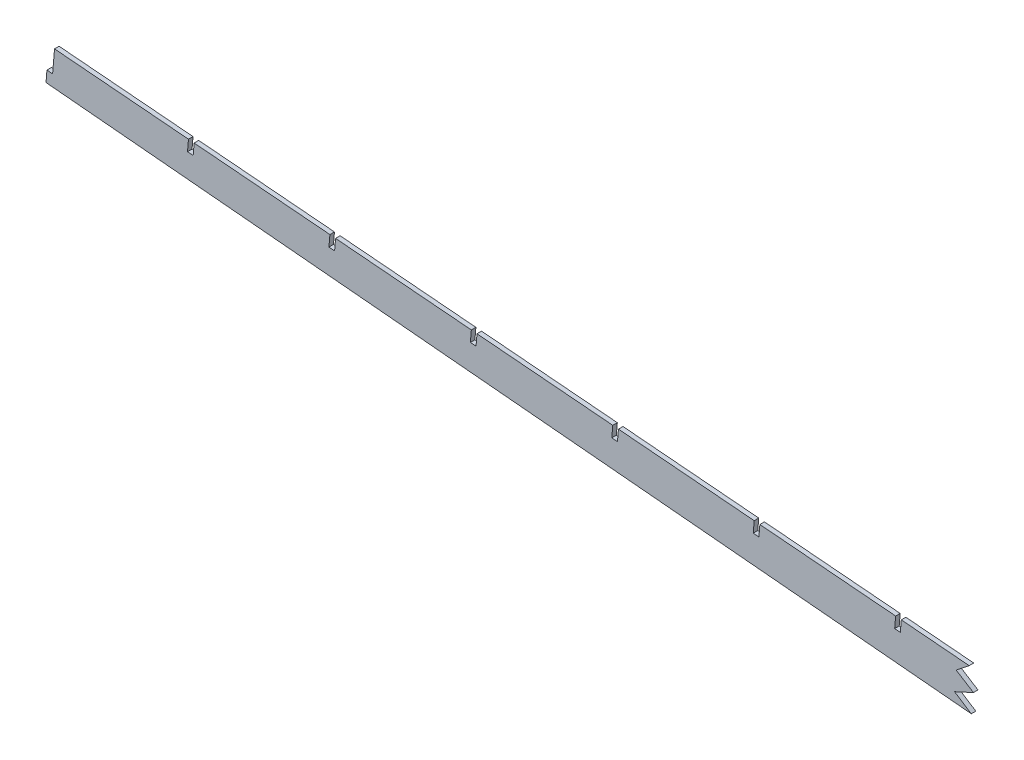
SolidWorks part; units mm, degrees
ref_plane "Front Plane" through (0, 0, 0) normal (0, 0, 1) x (1, 0, 0)
ref_plane "Top Plane" through (0, 0, 0) normal (0, 1, 0) x (1, 0, 0)
ref_plane "Right Plane" through (0, 0, 0) normal (1, 0, 0) x (0, 0, -1)
sketch "Sketch1" plane through (0, 0, 0) normal (0, 0, 1) x (1, 0, 0)
  line L0 (-949.6524, 80.0757) -> (-9.8872, -5.2596)
  line L1 (-945.9572, 86.1378) -> (-949.6524, 80.0757)
  line L8 (-6.7234, -5.5253) -> (-5.1293, 13.4579)
  line L9 (-5.1293, 13.4579) -> (-8.2932, 13.7235)
  line L10 (-8.2932, 13.7235) -> (-9.8872, -5.2596)
  line L11 (-9.8872, -5.2596) -> (-6.7234, -5.5253)
  line L12 (3.175, -5.8337) -> (3.175, 13.2163)
  line L13 (3.175, 13.2163) -> (0, 13.2163)
  line L14 (0, 13.2163) -> (0, -5.8337)
  line L15 (0, -5.8337) -> (3.175, -5.8337)
  line L17 (-943.1142, 119.9943) -> (-945.9572, 86.1378)
  line L18 (-945.9572, 86.1378) -> (-9.8872, -5.2596)
  line L19 (-6.7234, -5.5253) -> (0, -5.8337)
  line L20 (3.175, -5.8337) -> (152.4, -5.8337)
  line L21 (152.4, -5.8337) -> (152.4, 11.9463)
  line L22 (152.4, 11.9463) -> (69.85, 11.9463)
  line L23 (69.85, 11.9463) -> (25.4, 19.5663)
  line L24 (25.4, 19.5663) -> (-1.9861, 19.5663)
  line L25 (-1.9861, 19.5663) -> (-944.8986, 98.7448)
  line L26 (0, 13.2163) -> (0, 19.5663)
  line L27 (3.175, 13.2163) -> (3.175, 19.5663)
  line L28 (-5.1293, 13.4579) -> (-4.598, 19.7856)
  line L29 (-8.2932, 13.7235) -> (-7.7618, 20.0513)
  line L30 (-8.2932, 13.7235) -> (-945.4292, 92.426)
  line L31 (15.875, 19.5663) -> (15.875, 14.4863)
  line L32 (15.875, 14.4863) -> (19.05, 14.4863)
  line L33 (19.05, 14.4863) -> (19.05, 19.5663)
  line L34 (76.2, 6.8663) -> (76.2, 11.9463)
  line L35 (76.2, 6.8663) -> (79.375, 6.8663)
  line L36 (79.375, 6.8663) -> (79.375, 11.9463)
  line L37 (92.075, 11.9463) -> (92.075, 6.8663)
  line L38 (92.075, 6.8663) -> (95.25, 6.8663)
  line L39 (95.25, 6.8663) -> (95.25, 11.9463)
  line L40 (136.525, 11.9463) -> (136.525, 6.8663)
  line L41 (136.525, 6.8663) -> (139.7, 6.8663)
  line L42 (139.7, 6.8663) -> (139.7, 11.9463)
  line L44 (-949.6524, 80.0757) -> (-949.1211, 86.4035)
  line L45 (-949.1211, 86.4035) -> (-945.959, 86.1163)
  dimension "D1" = 25.4
  dimension "D2" = 6.35
extrude "Boss-Extrude1" add sketch "Sketch1" along normal blind 2.54
sketch "Sketch2" plane through (0, 0, 2.54) normal (0, 0, 1) x (1, 0, 0)
  line L1 (-76.483, 72.8473) -> (-82.5095, 1.0799)
  line L3 (-155.6446, 77.1971) -> (-161.4339, 8.255)
  line L5 (-234.8005, 81.6162) -> (-240.3617, 15.3891)
  line L7 (-313.9625, 85.9617) -> (-319.2865, 22.5591)
  line L9 (-393.1191, 90.3714) -> (-398.2146, 29.6908)
  line L11 (-472.2837, 94.686) -> (-477.1388, 36.8682)
  line L13 (-551.4418, 99.0783) -> (-556.0668, 44.0001)
  line L15 (-630.6082, 103.3716) -> (-634.991, 51.1773)
  line L17 (-709.7674, 107.7507) -> (-713.9195, 58.3043)
  line L19 (-788.9364, 112.0121) -> (-792.8436, 65.483)
  line L21 (-868.0976, 116.3681) -> (-871.7723, 72.6069)
  line L23 (-73.3191, 72.5816) -> (-79.3456, 0.8143)
  line L25 (-152.4808, 76.9314) -> (-158.27, 7.9893)
  line L27 (-231.6366, 81.3506) -> (-237.1978, 15.1234)
  line L29 (-310.7986, 85.696) -> (-316.1227, 22.2934)
  line L31 (-389.9552, 90.1057) -> (-395.0507, 29.4251)
  line L33 (-469.1198, 94.4203) -> (-473.9749, 36.6025)
  line L35 (-548.2779, 98.8126) -> (-552.903, 43.7344)
  line L37 (-627.4443, 103.1059) -> (-631.8272, 50.9116)
  line L39 (-706.6035, 107.485) -> (-710.7556, 58.0386)
  line L41 (-785.7726, 111.7464) -> (-789.6797, 65.2173)
  line L43 (-864.9337, 116.1024) -> (-868.6084, 72.3413)
  line L45 (-8.2932, 13.7235) -> (-945.4292, 92.426)
  line L47 (-7.7618, 20.0513) -> (-944.8986, 98.7448)
  line M27 (-7.7618, 20.0513) -> (-944.8986, 98.7448)
extrude "Cut-Extrude1" cut sketch "Sketch2" against normal through all and the other way through all contours L45 L43 L21 M27 | L45 L41 L19 M27 | L45 L39 L17 M27 | L45 L37 L15 M27 | L45 L35 L13 M27 | L45 L33 L11 M27 | L45 L31 L9 M27 | L45 L29 L7 M27 | L45 L27 L5 M27 | L45 L25 L3 M27 | L45 L23 L1 M27
sketch "Sketch3" plane through (0, 0, 2.54) normal (0, 0, 1) x (1, 0, 0)
  line L0 (-434.1875, 55.8592) -> (-441.4445, 50.0741)
  line L1 (-396.2844, 52.6764) -> (-472.0906, 59.042) construction
  line L2 (-441.4445, 50.0741) -> (-431.803, 44.0226)
  line L3 (-431.803, 44.0226) -> (-442.3497, 39.1715)
  line L4 (-442.3497, 39.1715) -> (-433.0143, 33.1624)
  line L5 (-949.6524, 80.0757) -> (-9.8872, -5.2596) construction
  line L6 (-434.1875, 55.8592) -> (201.2475, 33.1624)
  line L7 (201.2475, 33.1624) -> (148.3266, -67.6483)
  line L8 (148.3266, -67.6483) -> (-433.0143, 33.1624)
extrude "Cut-Extrude2" cut sketch "Sketch3" against normal blind 7.62 contours L8 L4 L3 L2 L0 L6 L7
